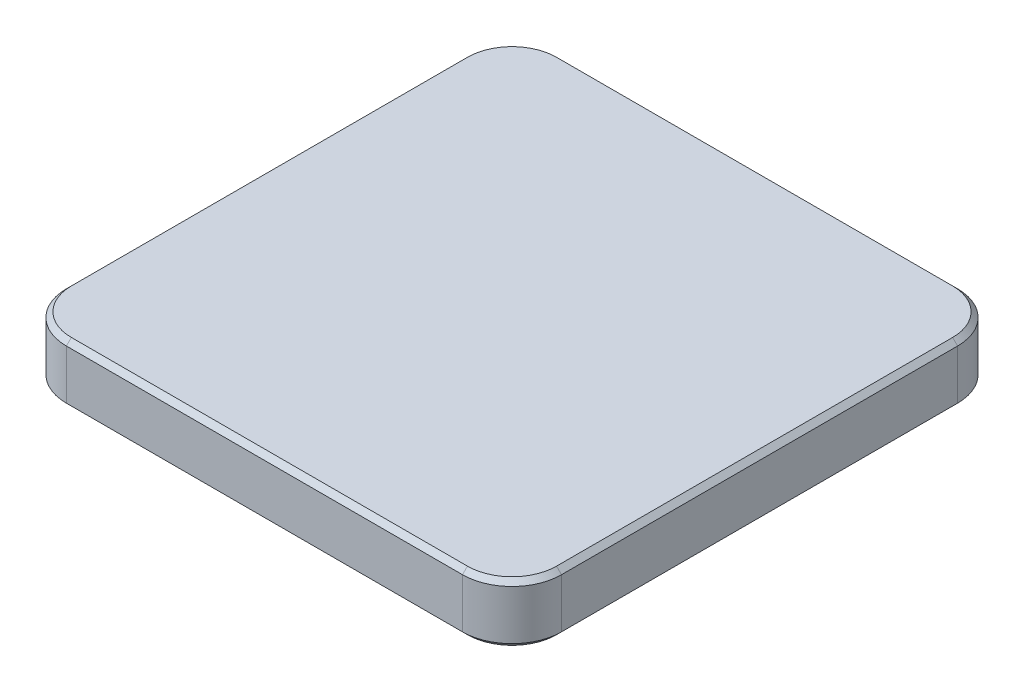
SolidWorks part; units mm, degrees
material "AISI 1020"
ref_plane "Alzado" through (0, 0, 0) normal (0, 0, 1) x (1, 0, 0)
ref_plane "Planta" through (0, 0, 0) normal (0, 1, 0) x (1, 0, 0)
ref_plane "Vista lateral" through (0, 0, 0) normal (1, 0, 0) x (0, 0, -1)
sketch "Croquis2" plane through (0, 0, 0) normal (0, 1, 0) x (1, 0, 0)
  line L1 (-40, -50) -> (40, -50)
  line L2 (-50, -40) -> (-50, 40)
  line L3 (-40, 50) -> (40, 50)
  line L4 (50, -40) -> (50, 40)
  line L5 (-50, -50) -> (50, 50) construction
  line L6 (-50, 50) -> (50, -50) construction
  arc A0 (-40, -50) -> (-50, -40) centre (-40, -40) cw
  arc A1 (40, -50) -> (50, -40) centre (40, -40) ccw
  arc A2 (40, 50) -> (50, 40) centre (40, 40) cw
  arc A3 (-50, 40) -> (-40, 50) centre (-40, 40) cw
  point P0 (0, 0)
  dimension "D3" = 10
  dimension "D1" = 100
  dimension "D2" = 100
extrude "Saliente-Extruir1" add sketch "Croquis2" along normal blind 12
chamfer "Chaflán1" distance 1 angle 45 16 edges at (-50, 12, 0) (-47.0711, 12, -47.0711) (0, 12, -50) (47.0711, 12, -47.0711) (50, 12, 0) (47.0711, 12, 47.0711) (0, 12, 50) (-47.0711, 12, 47.0711) (0, 0, 50) (47.0711, 0, 47.0711) (50, 0, 0) (47.0711, 0, -47.0711) (0, 0, -50) (-47.0711, 0, -47.0711) (-50, 0, 0) (-47.0711, 0, 47.0711)
